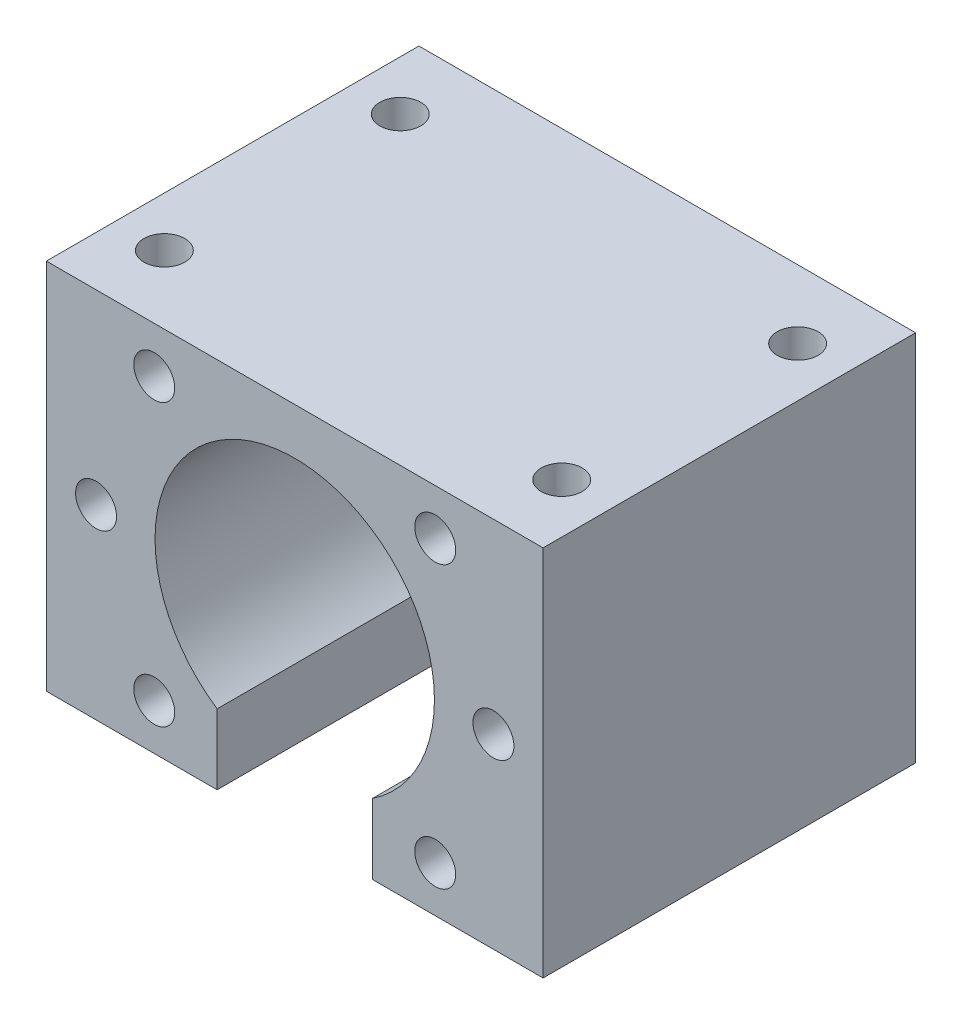
SolidWorks part; units mm, degrees
ref_plane "Ön Düzlem" through (0, 0, 0) normal (0, 0, 1) x (1, 0, 0)
ref_plane "Üst Düzlem" through (0, 0, 0) normal (0, 1, 0) x (1, 0, 0)
ref_plane "Sağ Düzlem" through (0, 0, 0) normal (1, 0, 0) x (0, 0, -1)
sketch "Çizim1" plane through (0, 0, 0) normal (0, 0, 1) x (1, 0, 0)
  line L1 (20, -15) -> (-20, -15)
  line L2 (20, -15) -> (20, 15)
  line L3 (20, 15) -> (-20, 15)
  line L4 (-20, -15) -> (-20, 15)
  line L5 (20, -15) -> (-20, 15) construction
  line L6 (20, 15) -> (-20, -15) construction
  point P0 (0, 0)
  dimension "D1" = 40
  dimension "D2" = 30
extrude "Yükseklik-Ekstrüzyon1" add sketch "Çizim1" against normal mid plane 30
sketch "Çizim2" plane through (0, 0, 15) normal (0, 0, 1) x (1, 0, 0)
  line L0 (0, 0) -> (0, -16.1468) construction
  line L1 (-6.25, -15) -> (-6.25, -9.3541)
  line L2 (-20, -15) -> (20, -15) construction
  line L3 (6.25, -15) -> (6.25, -9.3541)
  line L4 (-6.25, -15) -> (6.25, -15)
  arc A0 (6.25, -9.3541) -> (-6.25, -9.3541) centre (0, 0) ccw
  dimension "D1" = 22.5
  dimension "D2" = 6.25
extrude "Kes-Ekstrüzyon1" cut sketch "Çizim2" against normal blind 30
sketch "Çizim3" plane through (0, 0, 15) normal (0, 0, 1) x (1, 0, 0)
  line L0 (0, 0) -> (0, 6.8495) construction
  circle A0 centre (0, 0) radius 16 construction
  point P3 (-16, 0)
  point P4 (16, 0)
  point P5 (-11.3137, 11.3137)
  point P6 (11.3137, -11.3137)
  point P8 (0, 0)
  point P9 (-11.3137, -11.3137)
  point P10 (0, 0)
  point P11 (11.3137, 11.3137)
  dimension "D1" = 32
  dimension "D2" = 2
  dimension "D3" = 2
hole_wizard "M4 Tapa için Zıvana matkabı1" positions "3B Çizim1" profile "Çizim4" hole size "M4" standard "DIN"
sketch3d "3B Çizim1"
  point P0 (-11.3137, 11.3137, 15)
  point P3 (-16, 0, 15)
  point P6 (-11.3137, -11.3137, 15)
  point P9 (11.3137, -11.3137, 15)
  point P12 (16, 0, 15)
  point P15 (11.3137, 11.3137, 15)
sketch "Çizim4" plane through (-11.3137, 11.3137, 15) normal (1, 0, 0) x (0, -1, 0)
  line L0 (0, 0) -> (0, 15.9914)
  line L1 (0, 15.9914) -> (1.65, 15)
  line L2 (1.65, 15) -> (1.65, 0)
  line L5 (1.65, 0) -> (0, 0)
  line L10 (0, 15.9914) -> (-1.65, 15) construction
  line L11 (0, -6.35) -> (0, 107.95) construction
  dimension "Hole Dia." = 3.3
  dimension "Hole Depth" = 15
  dimension "Drill Angle" = 118
sketch "Çizim5" plane through (0, 15, 0) normal (0, 1, 0) x (1, 0, 0)
  line L0 (20, 15) -> (-20, 15) construction
  line L1 (-20, 15) -> (-20, -15) construction
  line L2 (20, 15) -> (20, -15) construction
  point P0 (-16, 9.5)
  point P1 (-16, -9.5)
  point P2 (16, -9.5)
  point P3 (16, 9.5)
  dimension "D1" = 5.5
  dimension "D2" = 5.5
  dimension "D3" = 4
  dimension "D4" = 4
  dimension "D5" = 4
  dimension "D6" = 19
  dimension "D7" = 4
  dimension "D8" = 19
hole_wizard "M4 Tapa için Zıvana matkabı3" positions "3B Çizim2" profile "Çizim6" hole size "M4" standard "DIN"
sketch3d "3B Çizim2"
  point P0 (-16, 15, -9.5)
  point P3 (-16, 15, 9.5)
  point P6 (16, 15, -9.5)
  point P9 (16, 15, 9.5)
sketch "Çizim6" plane through (-16, 15, -9.5) normal (1, 0, 0) x (0, 0, 1)
  line L0 (0, 0) -> (0, 13.9914)
  line L1 (0, 13.9914) -> (1.65, 13)
  line L2 (1.65, 13) -> (1.65, 0)
  line L5 (1.65, 0) -> (0, 0)
  line L10 (0, 13.9914) -> (-1.65, 13) construction
  line L11 (0, -6.35) -> (0, 107.95) construction
  dimension "Hole Dia." = 3.3
  dimension "Hole Depth" = 13
  dimension "Drill Angle" = 118
